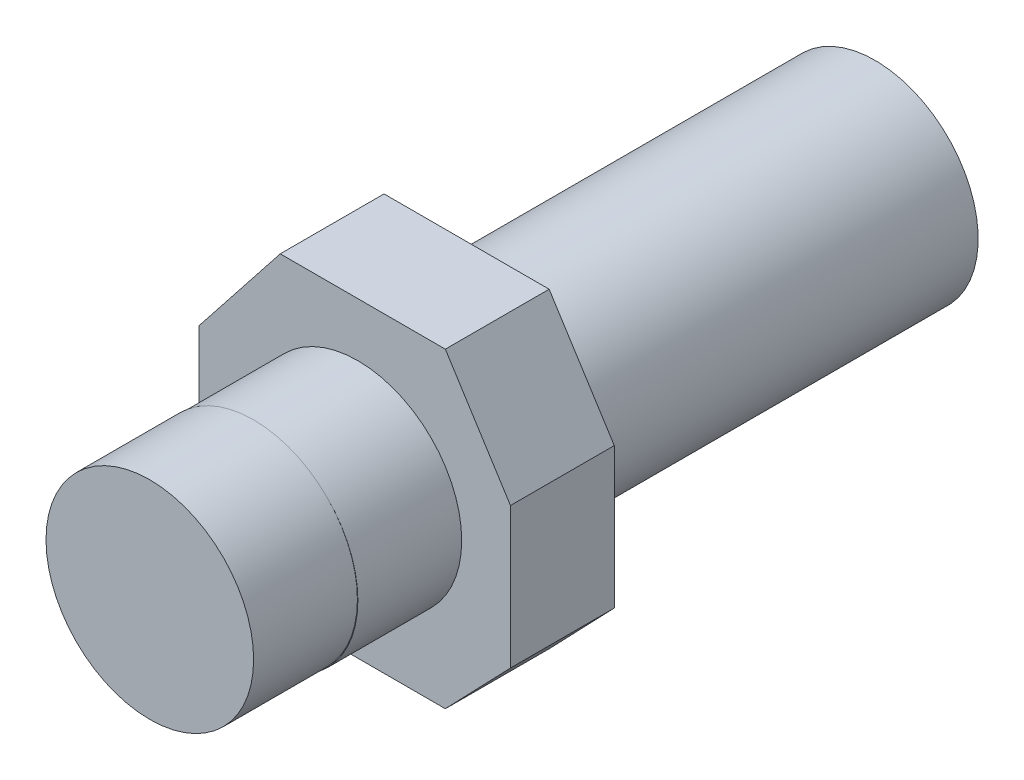
SolidWorks part; units mm, degrees
ref_plane "Front Plane" through (0, 0, 0) normal (0, 0, 1) x (1, 0, 0)
ref_plane "Top Plane" through (0, 0, 0) normal (0, 1, 0) x (1, 0, 0)
ref_plane "Right Plane" through (0, 0, 0) normal (1, 0, 0) x (0, 0, -1)
sketch "Sketch1" plane through (0, 0, 0) normal (0, 0, 1) x (1, 0, 0)
  line L4 (3.2151, 16.1664) -> (19.1208, 16.1664)
  line L5 (19.1208, 16.1664) -> (25.3926, 6.258)
  line L6 (25.3926, 6.258) -> (25.3926, -7.301)
  line L7 (25.3926, -7.301) -> (19.1208, -13.8336)
  line L8 (19.1208, -13.8336) -> (3.2151, -13.8336)
  line L9 (3.2151, -13.8336) -> (-4.6074, -7.301)
  line L10 (-4.6074, -7.301) -> (-4.6074, 6.258)
  line L11 (-4.6074, 6.258) -> (3.2151, 16.1664)
  point P6 (25.3926, 11.2122)
extrude "Boss-Extrude1" add sketch "Sketch1" along normal blind 10
sketch "Sketch2" plane through (0, 0, 10) normal (0, 0, 1) x (1, 0, 0)
  circle A0 centre (10.6959, 0.9932) radius 10
extrude "Boss-Extrude2" add sketch "Sketch2" along normal blind 10
sketch "Sketch3" plane through (0, 0, 20) normal (0, 0, 1) x (1, 0, 0)
  circle A0 centre (10.6525, 1.0365) radius 10
extrude "Boss-Extrude3" add sketch "Sketch3" along normal blind 10 contours A0
sketch "Sketch4" plane through (0, 0, 0) normal (0, 0, -1) x (-1, 0, 0)
  circle A0 centre (-10.5226, 1.0365) radius 9.925
  point P2 (-10.5226, 1.0365)
extrude "Boss-Extrude4" add sketch "Sketch4" along normal blind 40
